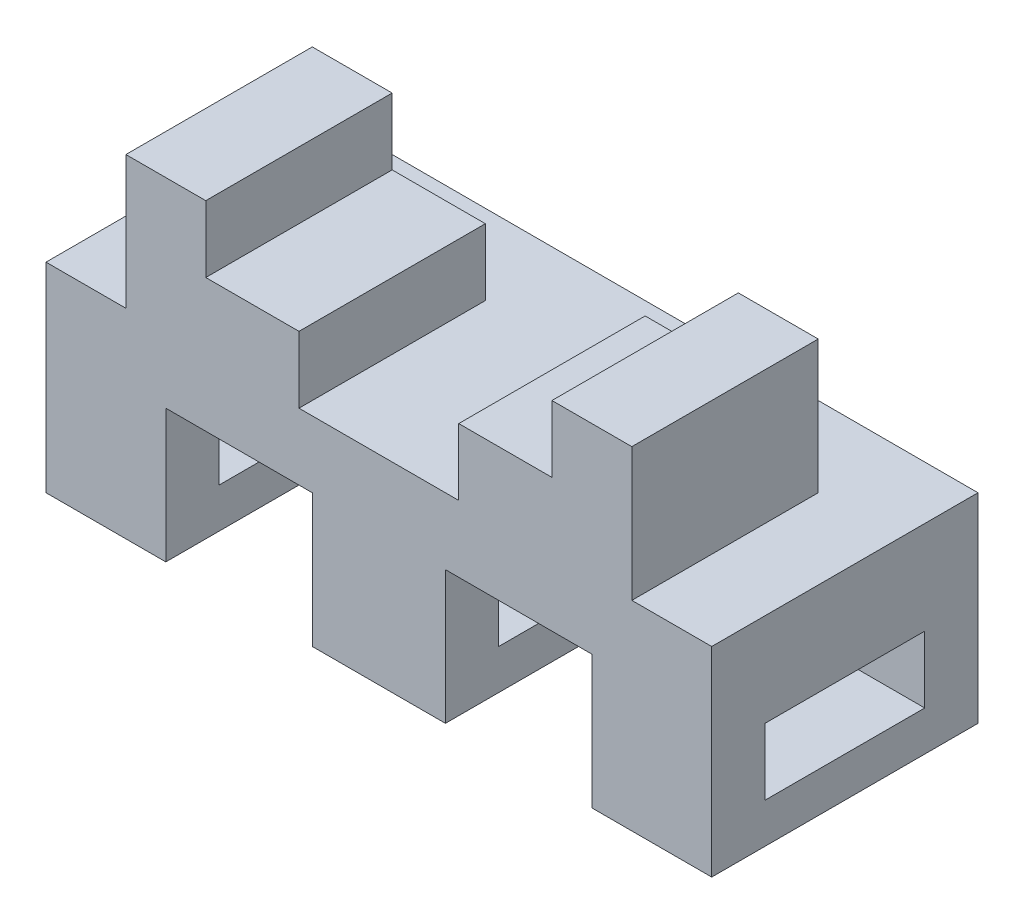
SolidWorks part; units mm, degrees
ref_plane "Front Plane" through (0, 0, 0) normal (0, 0, 1) x (1, 0, 0)
ref_plane "Top Plane" through (0, 0, 0) normal (0, 1, 0) x (1, 0, 0)
ref_plane "Right Plane" through (0, 0, 0) normal (1, 0, 0) x (0, 0, -1)
sketch "Sketch1" plane through (0, 0, 0) normal (0, 1, 0) x (1, 0, 0)
  line L1 (0, 23.5471) -> (-22.3946, 7.2765)
  line L2 (-22.3946, 7.2765) -> (-13.8406, -19.05)
  line L3 (-13.8406, -19.05) -> (13.8406, -19.05)
  line L4 (13.8406, -19.05) -> (22.3946, 7.2765)
  line L5 (22.3946, 7.2765) -> (0, 23.5471)
  line L29 (-69.9685, 0) -> (69.9685, 0) construction
  line L30 (0, -62.6988) -> (0, 62.6988) construction
  line L31 (-65.3552, 38.1) -> (65.3552, 38.1) construction
  line L32 (-80.0763, -38.1) -> (-25.4, -38.1) construction
  line L33 (-38.1, -55.2993) -> (-38.1, -25.4) construction
  line L34 (38.1, -56.3951) -> (38.1, 56.3951) construction
  line L36 (38.1, 45.4323) -> (31.75, 41.7662)
  line L37 (31.75, 41.7662) -> (31.75, 34.4338)
  line L38 (31.75, 34.4338) -> (38.1, 30.7677)
  line L39 (38.1, 30.7677) -> (44.45, 34.4338)
  line L40 (44.45, 34.4338) -> (44.45, 41.7662)
  line L41 (44.45, 41.7662) -> (38.1, 45.4323)
  line L42 (38.1, -30.7677) -> (31.75, -34.4338)
  line L43 (31.75, -34.4338) -> (31.75, -41.7662)
  line L44 (31.75, -41.7662) -> (38.1, -45.4323)
  line L45 (38.1, -45.4323) -> (44.45, -41.7662)
  line L46 (44.45, -41.7662) -> (44.45, -34.4338)
  line L47 (44.45, -34.4338) -> (38.1, -30.7677)
  line L48 (-38.1, -30.7677) -> (-44.45, -34.4338)
  line L49 (-44.45, -34.4338) -> (-44.45, -41.7662)
  line L50 (-44.45, -41.7662) -> (-38.1, -45.4323)
  line L51 (-38.1, -45.4323) -> (-31.75, -41.7662)
  line L52 (-31.75, -41.7662) -> (-31.75, -34.4338)
  line L53 (-31.75, -34.4338) -> (-38.1, -30.7677)
  line L54 (-38.1, 45.4323) -> (-44.45, 41.7662)
  line L55 (-44.45, 41.7662) -> (-44.45, 34.4338)
  line L56 (-44.45, 34.4338) -> (-38.1, 30.7677)
  line L57 (-38.1, 30.7677) -> (-31.75, 34.4338)
  line L58 (-31.75, 34.4338) -> (-31.75, 41.7662)
  line L59 (-31.75, 41.7662) -> (-38.1, 45.4323)
  line L75 (-44.45, -27.1015) -> (-44.45, 27.1015)
  line L76 (-23.6985, 44.45) -> (23.6985, 44.45)
  line L77 (44.45, 27.1015) -> (44.45, -27.1015)
  line L78 (23.6985, -44.45) -> (-23.6985, -44.45)
  line L79 (-38.1, 25.4) -> (-38.1, 55.2993) construction
  line L80 (-38.1, 52.7647) -> (-50.8, 45.4323)
  line L81 (-50.8, 45.4323) -> (-50.8, 30.7677)
  line L82 (-50.8, 30.7677) -> (-44.45, 27.1015)
  line L85 (-23.6985, 44.45) -> (-38.1, 52.7647)
  line L86 (38.1, 52.7647) -> (23.6985, 44.45)
  line L89 (44.45, 27.1015) -> (50.8, 30.7677)
  line L90 (50.8, 30.7677) -> (50.8, 45.4323)
  line L91 (50.8, 45.4323) -> (38.1, 52.7647)
  line L92 (38.1, -52.7647) -> (50.8, -45.4323)
  line L93 (50.8, -45.4323) -> (50.8, -30.7677)
  line L94 (50.8, -30.7677) -> (44.45, -27.1015)
  line L97 (23.6985, -44.45) -> (38.1, -52.7647)
  line L98 (-38.1, -52.7647) -> (-23.6985, -44.45)
  line L101 (-44.45, -27.1015) -> (-50.8, -30.7677)
  line L102 (-50.8, -30.7677) -> (-50.8, -45.4323)
  line L103 (-50.8, -45.4323) -> (-38.1, -52.7647)
  line L104 (-38.1, 23.4353) -> (-31.75, 27.1015)
  line L105 (31.75, 27.1015) -> (38.1, 23.4353)
  line L106 (38.1, 25.4) -> (38.1, 56.3951) construction
  line L107 (25.4, 45.4323) -> (25.4, 44.9341)
  line L108 (-25.4, 44.9341) -> (-25.4, 45.4323)
  line L109 (-38.1, -23.4353) -> (-38.1, 23.4353) construction
  line L110 (-25.4, -30.7677) -> (-31.75, -27.1015)
  line L111 (0, -38.1) -> (80.0763, -38.1) construction
  line L112 (38.1, -23.4353) -> (31.75, -27.1015)
  line L113 (25.4, -43.9659) -> (25.4, -45.4323)
  line L114 (-25.4, -45.4323) -> (-25.4, -43.9659)
  line L115 (-88.9, 25.4) -> (88.9, 25.4) construction
  circle A0 centre (0, 0) radius 19.05 construction
  circle A5 centre (38.1, 0) radius 3.175
  circle A6 centre (-38.1, 0) radius 3.175
  circle A7 centre (38.1, 38.1) radius 6.35 construction
  circle A8 centre (38.1, -38.1) radius 6.35 construction
  circle A9 centre (-38.1, -38.1) radius 6.35 construction
  circle A10 centre (-38.1, 38.1) radius 6.35 construction
  circle A11 centre (-38.1, 38.1) radius 12.7 construction
  circle A12 centre (38.1, 38.1) radius 12.7 construction
  circle A13 centre (38.1, -38.1) radius 12.7 construction
  circle A14 centre (-38.1, -38.1) radius 12.7 construction
  point P7 (-38.1, -38.1)
  point P10 (-38.1, 38.1)
  point P19 (38.1, 38.1)
  point P20 (38.1, -38.1)
  point P21 (-38.1, -38.1)
  point P43 (0, 0)
  point P46 (0, 38.1)
  point P50 (0, 0)
  point P52 (0, -38.1)
  point P57 (-38.1, 0)
  point P58 (38.1, 0)
  point P87 (0, 0)
  point P95 (0, 25.4)
  point P98 (38.1, 16.3535)
  point P107 (0, 0)
  point P108 (0, 0)
  point P111 (38.1, 55.2993)
  dimension "D1" = 38.1
  dimension "D2" = 12.7
  dimension "D3" = 38.1
  dimension "D4" = 12.7
  dimension "D5" = 12.7
  dimension "D10" = 6.35
  dimension "D11" = 6.35
  dimension "D6" = 12.7
  dimension "D14" = 25.4
  dimension "D15" = 25.4
  dimension "D16" = 25.4
  dimension "D17" = 25.4
  dimension "D7" = 38.1
  dimension "D8" = 76.2
  dimension "D9" = 76.2
  dimension "D13" = 88.9
  dimension "D12" = 88.9
  dimension "D18" = 44.45
  dimension "D19" = 44.45
sketch "Sketch2" plane through (0, 0, 0) normal (0, 1, 0) x (1, 0, 0)
  line L1 (-63.5, -25.4) -> (63.5, -25.4)
  line L2 (-63.5, -25.4) -> (-63.5, 25.4)
  line L3 (-63.5, 25.4) -> (63.5, 25.4)
  line L4 (63.5, -25.4) -> (63.5, 25.4)
  line L5 (-63.5, -25.4) -> (63.5, 25.4) construction
  line L6 (-63.5, 25.4) -> (63.5, -25.4) construction
  point P0 (0, 0)
  dimension "D1" = 50.8
  dimension "D2" = 127
extrude "Boss-Extrude1" add sketch "Sketch2" along normal blind 38.1
sketch "Sketch4" plane through (0, 0, 0) normal (0, 0, 1) x (1, 0, 0)
  line L0 (-40.64, 0) -> (-40.64, 25.4)
  line L1 (-63.5, 0) -> (63.5, 0) construction
  line L2 (-40.64, 25.4) -> (-12.7, 25.4)
  line L3 (-12.7, 25.4) -> (-12.7, 0)
  line L4 (12.7, 0) -> (12.7, 25.4)
  line L5 (12.7, 25.4) -> (40.64, 25.4)
  line L6 (40.64, 25.4) -> (40.64, 0)
  line L7 (-63.5, 38.1) -> (-63.5, 0) construction
  line L8 (63.5, 38.1) -> (63.5, 0) construction
  line L9 (-40.64, 0) -> (-12.7, 0)
  line L10 (12.7, 0) -> (40.64, 0)
  dimension "D1" = 22.86
  dimension "D2" = 25.4
  dimension "D3" = 27.94
  dimension "D4" = 27.94
  dimension "D5" = 22.86
  dimension "D6" = 25.4
extrude "Cut-Extrude1" cut sketch "Sketch4" against normal through all both and the other way through all
sketch "Sketch5" plane through (0, 0, 0) normal (1, 0, 0) x (0, 0, -1)
  line L0 (-25.4, 0) -> (25.4, 0) construction
  line L1 (-15.24, 20.32) -> (15.24, 20.32)
  line L2 (-15.24, 20.32) -> (-15.24, 7.62)
  line L3 (-15.24, 7.62) -> (15.24, 7.62)
  line L4 (15.24, 20.32) -> (15.24, 7.62)
  line L5 (0, 38.1) -> (0, 0.3448) construction
  line L6 (-25.4, 38.1) -> (25.4, 38.1) construction
  dimension "D1" = 12.7
  dimension "D2" = 30.48
  dimension "D3" = 7.62
extrude "Cut-Extrude2" cut sketch "Sketch5" against normal through all both and the other way through all contours L2 L1 L4 L3
sketch "Sketch7" plane through (0, 0, -25.4) normal (0, 0, -1) x (-1, 0, 0)
  line L0 (48.26, 38.1) -> (48.26, 63.5)
  line L1 (-63.5, 38.1) -> (63.5, 38.1) construction
  line L2 (48.26, 63.5) -> (33.02, 63.5)
  line L3 (33.02, 63.5) -> (33.02, 50.8)
  line L4 (33.02, 50.8) -> (15.24, 50.8)
  line L5 (15.24, 50.8) -> (15.24, 38.1)
  line L6 (15.24, 38.1) -> (48.26, 38.1)
  line L7 (63.5, 38.1) -> (63.5, 0) construction
  line L8 (0, 38.1) -> (0, 70.7224) construction
  line L9 (-15.24, 38.1) -> (-48.26, 38.1)
  line L10 (-15.24, 50.8) -> (-15.24, 38.1)
  line L11 (-33.02, 50.8) -> (-15.24, 50.8)
  line L12 (-33.02, 63.5) -> (-33.02, 50.8)
  line L13 (-48.26, 63.5) -> (-33.02, 63.5)
  line L14 (-48.26, 38.1) -> (-48.26, 63.5)
  dimension "D1" = 25.4
  dimension "D2" = 15.24
  dimension "D3" = 12.7
  dimension "D4" = 33.02
  dimension "D5" = 15.24
extrude "Boss-Extrude2" add sketch "Sketch7" along normal blind 35.56 from surface at -50.8 starting at face at (0, 14.8167, 25.4)
equation "\"Length\" = 5"
equation "\"D2@Sketch2\"=\"Length\""
